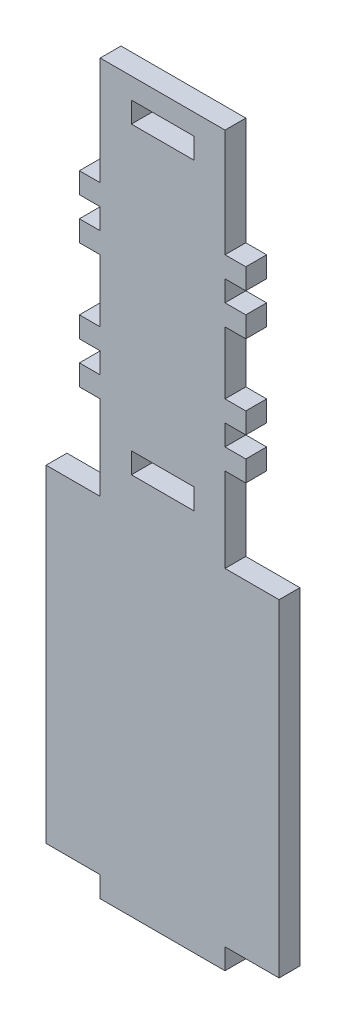
SolidWorks part; units mm, degrees
ref_plane "Front Plane" through (0, 0, 0) normal (0, 0, 1) x (1, 0, 0)
ref_plane "Top Plane" through (0, 0, 0) normal (0, 1, 0) x (1, 0, 0)
ref_plane "Right Plane" through (0, 0, 0) normal (1, 0, 0) x (0, 0, -1)
sketch "Sketch1" plane through (0, 0, 0) normal (0, 0, 1) x (1, 0, 0)
  line L0 (0, 219.075) -> (0, 116.2307) construction
  line L1 (19.05, -3.175) -> (-19.05, -3.175)
  line L2 (19.05, -3.175) -> (19.05, 3.175)
  line L4 (-19.05, -3.175) -> (-19.05, 3.175)
  line L5 (19.05, -3.175) -> (-19.05, 3.175) construction
  line L6 (19.05, 3.175) -> (-19.05, -3.175) construction
  line L7 (-35.56, 3.175) -> (-19.05, 3.175)
  line L8 (-35.56, 3.175) -> (-35.56, 219.075)
  line L9 (-35.56, 219.075) -> (35.56, 219.075)
  line L10 (35.56, 3.175) -> (35.56, 219.075)
  line L11 (19.05, 3.175) -> (35.56, 3.175)
  line L13 (9.525, 206.375) -> (-9.525, 206.375)
  line L14 (9.525, 206.375) -> (9.525, 212.725)
  line L15 (9.525, 212.725) -> (-9.525, 212.725)
  line L16 (-9.525, 206.375) -> (-9.525, 212.725)
  line L17 (9.525, 206.375) -> (-9.525, 212.725) construction
  line L18 (9.525, 212.725) -> (-9.525, 206.375) construction
  line L19 (9.525, 113.665) -> (-9.525, 113.665)
  line L20 (9.525, 113.665) -> (9.525, 120.015)
  line L21 (9.525, 120.015) -> (-9.525, 120.015)
  line L22 (-9.525, 113.665) -> (-9.525, 120.015)
  line L23 (9.525, 113.665) -> (-9.525, 120.015) construction
  line L24 (9.525, 120.015) -> (-9.525, 113.665) construction
  point P0 (0, 0)
  point P12 (0, 209.55)
  point P17 (0, 116.84)
  dimension "D1" = 38.1
  dimension "D2" = 6.35
  dimension "D3" = 0
  dimension "D4" = 215.9
  dimension "D5" = 6.35
  dimension "D6" = 71.12
  dimension "D7" = 19.05
  dimension "D8" = 6.35
  dimension "D9" = 19.05
  dimension "D10" = 86.36
  dimension "D11" = 6.35
  dimension "D12" = 16.51
extrude "Boss-Extrude1" add sketch "Sketch1" along normal blind 6.35
sketch "Sketch3" plane through (0, 0, 0) normal (0, 0, -1) x (-1, 0, 0)
  line L0 (0, 219.075) -> (0, 130.7051) construction
  line L1 (-35.56, 219.075) -> (-19.05, 219.075)
  line L2 (-35.56, 219.075) -> (-35.56, 103.1875)
  line L3 (-35.56, 103.1875) -> (-19.05, 103.1875)
  line L4 (-19.05, 219.075) -> (-19.05, 186.1084)
  line L5 (-35.56, 219.075) -> (35.56, 219.075) construction
  line L6 (35.56, 103.1875) -> (19.05, 103.1875)
  line L7 (19.05, 219.075) -> (19.05, 186.1084)
  line L8 (35.56, 219.075) -> (19.05, 219.075)
  line L9 (35.56, 219.075) -> (35.56, 103.1875)
  line L11 (-19.05, 128.9584) -> (-25.4, 128.9584)
  line L13 (-19.05, 135.3084) -> (-25.4, 135.3084)
  line L14 (-25.4, 128.9584) -> (-25.4, 135.3084)
  line L15 (-19.05, 141.6584) -> (-25.4, 141.6584)
  line L16 (-25.4, 141.6584) -> (-25.4, 148.0084)
  line L17 (-19.05, 148.0084) -> (-25.4, 148.0084)
  line L19 (-19.05, 186.1084) -> (-25.4, 186.1084)
  line L20 (-25.4, 179.7584) -> (-25.4, 186.1084)
  line L21 (-19.05, 179.7584) -> (-25.4, 179.7584)
  line L23 (-19.05, 167.0584) -> (-25.4, 167.0584)
  line L24 (-25.4, 167.0584) -> (-25.4, 173.4084)
  line L25 (-19.05, 173.4084) -> (-25.4, 173.4084)
  line L26 (19.05, 135.3084) -> (25.4, 135.3084)
  line L27 (25.4, 128.9584) -> (25.4, 135.3084)
  line L28 (19.05, 128.9584) -> (25.4, 128.9584)
  line L30 (19.05, 141.6584) -> (25.4, 141.6584)
  line L31 (25.4, 141.6584) -> (25.4, 148.0084)
  line L32 (19.05, 148.0084) -> (25.4, 148.0084)
  line L34 (19.05, 167.0584) -> (25.4, 167.0584)
  line L35 (25.4, 167.0584) -> (25.4, 173.4084)
  line L36 (19.05, 173.4084) -> (25.4, 173.4084)
  line L38 (19.05, 179.7584) -> (25.4, 179.7584)
  line L39 (25.4, 179.7584) -> (25.4, 186.1084)
  line L40 (19.05, 186.1084) -> (25.4, 186.1084)
  line L42 (-19.05, 179.7584) -> (-19.05, 173.4084)
  line L45 (-19.05, 167.0584) -> (-19.05, 148.0084)
  line L47 (-19.05, 141.6584) -> (-19.05, 135.3084)
  line L48 (19.05, 128.9584) -> (19.05, 103.1875)
  line L49 (19.05, 141.6584) -> (19.05, 135.3084)
  line L50 (19.05, 167.0584) -> (19.05, 148.0084)
  line L51 (19.05, 179.7584) -> (19.05, 173.4084)
  line L52 (-19.05, 128.9584) -> (-19.05, 103.1875)
  dimension "D1" = 38.1
  dimension "D2" = 6.35
  dimension "D3" = 6.35
  dimension "D4" = 2
  dimension "D5" = 2
extrude "Cut-Extrude1" cut sketch "Sketch3" against normal blind 6.35
